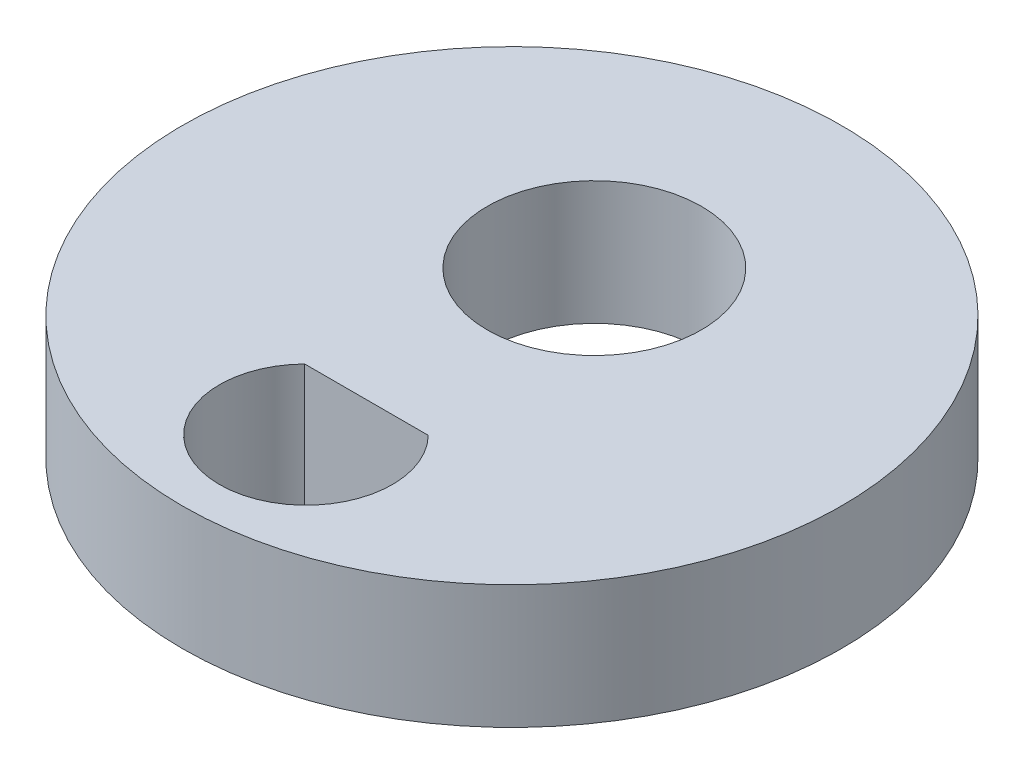
SolidWorks part; units mm, degrees
ref_plane "Front Plane" through (0, 0, 0) normal (0, 0, 1) x (1, 0, 0)
ref_plane "Top Plane" through (0, 0, 0) normal (0, 1, 0) x (1, 0, 0)
ref_plane "Right Plane" through (0, 0, 0) normal (1, 0, 0) x (0, 0, -1)
sketch "Sketch1" plane through (0, 0, 0) normal (0, 1, 0) x (1, 0, 0)
  line L2 (1.5, -3.5303) -> (-1.5, -3.5303)
  circle A0 centre (0, 0) radius 8
  arc A1 (-1.5, -3.5303) -> (1.5, -3.5303) centre (0, -5) ccw
  circle A2 centre (0, 2) radius 2.6
  point P5 (0, 0)
  dimension "D1" = 16
  dimension "D3" = 3
  dimension "D2" = 2.1
  dimension "D5" = 5.2
  dimension "3" = 5
  dimension "D6" = 2
extrude "Boss-Extrude1" add sketch "Sketch1" along normal blind 3
